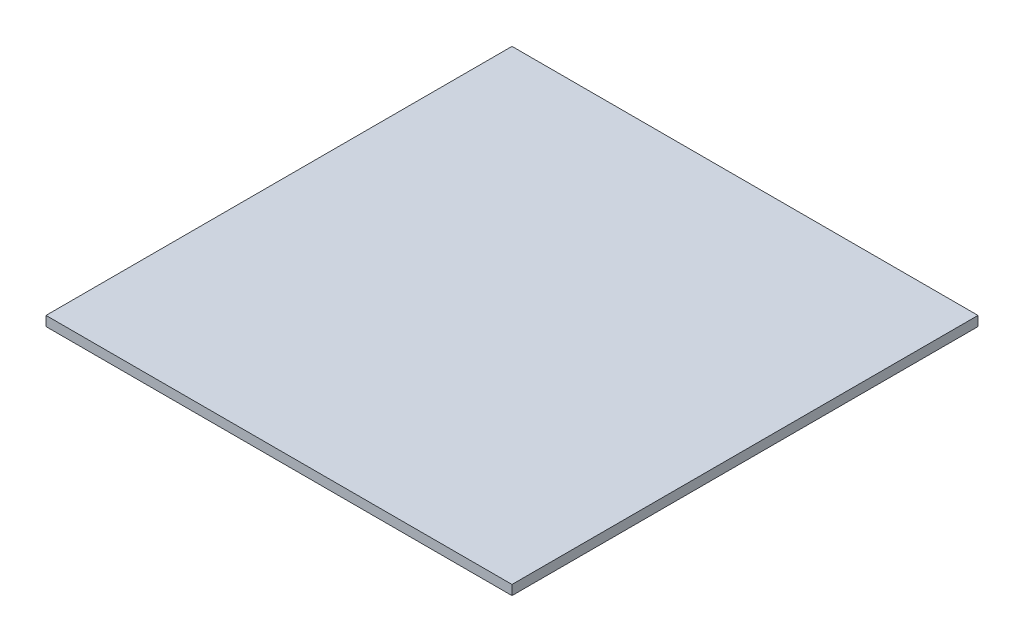
SolidWorks part; units mm, degrees
material "Acrylic (Medium-high impact)"
ref_plane "Front Plane" through (0, 0, 0) normal (0, 0, 1) x (1, 0, 0)
ref_plane "Top Plane" through (0, 0, 0) normal (0, 1, 0) x (1, 0, 0)
ref_plane "Right Plane" through (0, 0, 0) normal (1, 0, 0) x (0, 0, -1)
sketch "Sketch1" plane through (0, 0, 0) normal (0, 1, 0) x (1, 0, 0)
  line L1 (-152.4, -152.4) -> (152.4, -152.4)
  line L2 (-152.4, -152.4) -> (-152.4, 152.4)
  line L3 (-152.4, 152.4) -> (152.4, 152.4)
  line L4 (152.4, -152.4) -> (152.4, 152.4)
  line L5 (-152.4, -152.4) -> (152.4, 152.4) construction
  line L6 (-152.4, 152.4) -> (152.4, -152.4) construction
  point P0 (0, 0)
  dimension "D1" = 304.8
  dimension "D2" = 304.8
extrude "Boss-Extrude1" add sketch "Sketch1" along normal blind 6.35
